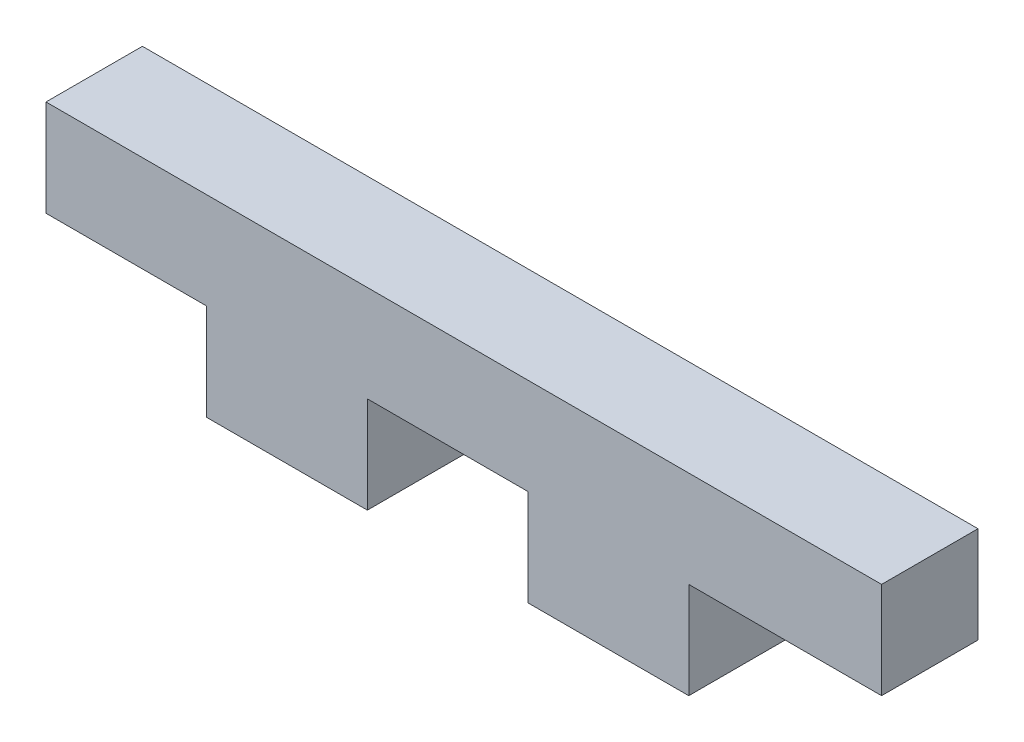
SolidWorks part; units mm, degrees
ref_plane "Plan de face" through (0, 0, 0) normal (0, 0, 1) x (1, 0, 0)
ref_plane "Plan de dessus" through (0, 0, 0) normal (0, 1, 0) x (1, 0, 0)
ref_plane "Plan de droite" through (0, 0, 0) normal (1, 0, 0) x (0, 0, -1)
sketch "Esquisse1" plane through (0, 0, 0) normal (0, 0, 1) x (1, 0, 0)
  line L1 (3.9901, 0.1004) -> (8.9901, 0.1004)
  line L2 (3.9901, 0.1004) -> (3.9901, -2.8996)
  line L3 (3.9901, -2.8996) -> (8.9901, -2.8996)
  line L4 (8.9901, 0.1004) -> (8.9901, -2.8996)
  line L5 (24.9901, 3.1004) -> (-1.0099, 3.1004)
  line L6 (24.9901, 3.1004) -> (24.9901, 0.1004)
  line L7 (24.9901, 0.1004) -> (-1.0099, 0.1004)
  line L8 (-1.0099, 3.1004) -> (-1.0099, 0.1004)
  line L9 (13.9901, 0.1004) -> (18.9901, 0.1004)
  line L10 (13.9901, 0.1004) -> (13.9901, -2.8996)
  line L11 (13.9901, -2.8996) -> (18.9901, -2.8996)
  line L12 (18.9901, 0.1004) -> (18.9901, -2.8996)
  dimension "D1" = 3
  dimension "D2" = 26
  dimension "D3" = 5
  dimension "D4" = 5
  dimension "D5" = 3
  dimension "D6" = 3
  dimension "D7" = 5
  dimension "D8" = 5
extrude "Boss.-Extru.1" add sketch "Esquisse1" along normal blind 3 contours L4 L1 L2 L3 | L12 L7 L10 L11 | L5 L8 L7 L1 L6
